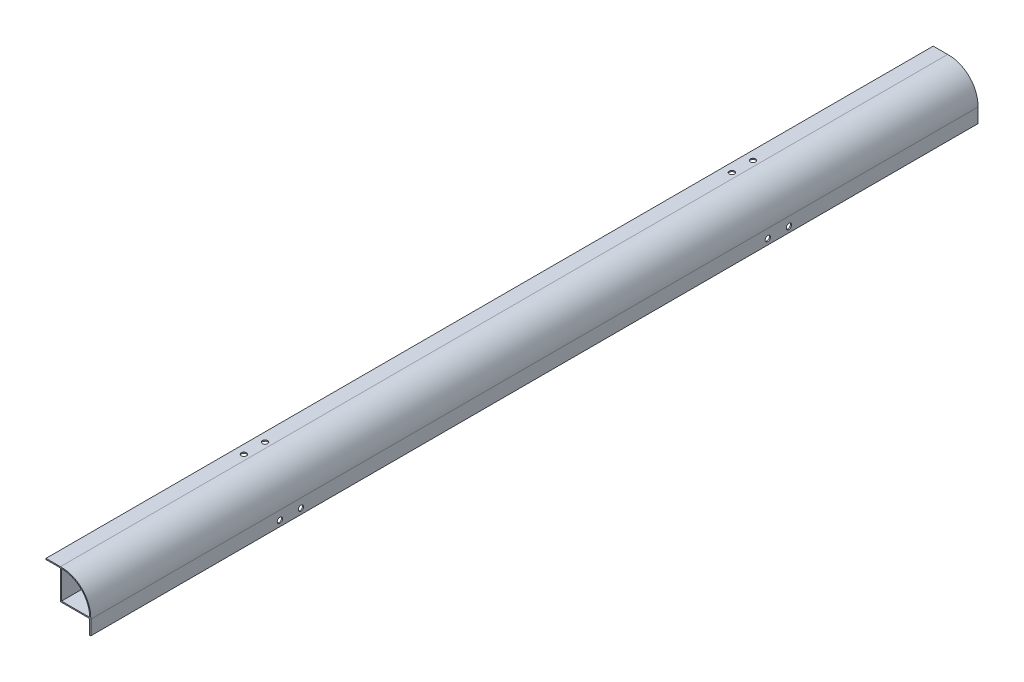
SolidWorks part; units mm, degrees
ref_plane "Alzado" through (0, 0, 0) normal (0, 0, 1) x (1, 0, 0)
ref_plane "Planta" through (0, 0, 0) normal (0, 1, 0) x (1, 0, 0)
ref_plane "Vista lateral" through (0, 0, 0) normal (1, 0, 0) x (0, 0, -1)
sketch "Croquis1" plane through (0, 0, 0) normal (0, 0, 1) x (1, 0, 0)
  line L0 (-13.7, -13.7) -> (13.6811, -13.7)
  line L1 (-12.7, -12.7) -> (12.7, -12.7)
  line L2 (-12.7, -12.7) -> (-12.7, 12.7)
  line L5 (0, 16.5842) -> (0, -23.118) construction
  line L6 (-13.7, -13.7) -> (-13.7, 13.6811)
  line L8 (-18.0998, 0) -> (17.5647, 0) construction
  line L9 (13.6811, -13.7) -> (12.6811, -13.7)
  line L10 (13.6811, -13.7) -> (13.6811, -26.7)
  line L11 (13.6811, -26.7) -> (12.6811, -26.7)
  line L12 (12.6811, -13.7) -> (12.6811, -26.7)
  line L13 (-13.7, 13.6811) -> (-26.7, 13.6811)
  line L14 (-13.7, 13.6811) -> (-13.7, 12.6811)
  line L15 (-13.7, 12.6811) -> (-26.7, 12.6811)
  line L16 (-26.7, 13.6811) -> (-26.7, 12.6811)
  arc A0 (-12.7, 12.7) -> (12.7, -12.7) centre (-12.7, -12.7) cw
  arc A1 (-13.7, 13.6811) -> (13.6811, -13.7) centre (-12.7, -12.7) cw
  point P0 (0, 0)
  point P12 (-12.7, 0)
  point P13 (0, -12.7)
  dimension "D3" = 25.4
  dimension "D1" = 25.4
  dimension "D2" = 25.4
  dimension "D5" = 1
  dimension "D6" = 13
  dimension "D7" = 1
  dimension "D8" = 13
  dimension "D4" = 1
extrude "Saliente-Extruir1" add sketch "Croquis1" along normal mid plane 800 contours A1 L6 L0 L2 A0 L1 | L13 L16 L15 L6 | L0 L12 L11 L10
sketch "Croquis2" plane through (0, 13.6811, 0) normal (0, 1, 0) x (1, 0, 0)
  line L0 (119.3875, 0) -> (-118.4797, 0) construction
  line L1 (-29.9629, -220) -> (20.492, -220) construction
  line L2 (-26.7, -400) -> (-26.7, 400) construction
  line L3 (-13.7, -400) -> (13.7, -400) construction
  line L4 (-29.9629, 220) -> (20.492, 220) construction
  circle A0 centre (-18.7, -210.5) radius 2.3813
  circle A1 centre (-18.7, -229.5) radius 2.3813
  circle A2 centre (-18.7, 229.5) radius 2.3813
  circle A3 centre (-18.7, 210.5) radius 2.3813
  dimension "D1" = 4.7625
  dimension "D2" = 9.5
  dimension "D3" = 8
  dimension "D4" = 180
extrude "Cortar-Extruir1" cut sketch "Croquis2" against normal blind 10
sketch "Croquis3" plane through (13.6811, 0, 0) normal (1, 0, 0) x (0, 0, -1)
  line L0 (0, 76.9116) -> (0, -92.6451) construction
  line L1 (-220, 38.7463) -> (-220, -62.7421) construction
  line L2 (-400, 13.7) -> (-400, -13.7) construction
  line L3 (-400, -26.7) -> (400, -26.7) construction
  line L4 (220, 38.7463) -> (220, -62.7421) construction
  circle A0 centre (-210.5, -21.7) radius 2.3813
  circle A1 centre (-229.5, -21.7) radius 2.3813
  circle A2 centre (-210.5, -21.7) radius 2.3813
  circle A3 centre (-229.5, -21.7) radius 2.3813
  circle A4 centre (229.5, -21.7) radius 2.3813
  circle A5 centre (210.5, -21.7) radius 2.3813
  dimension "D1" = 4.7625
  dimension "D2" = 180
  dimension "D3" = 9.5
  dimension "D4" = 5
extrude "Cortar-Extruir2" cut sketch "Croquis3" against normal blind 10 contours A1 | A0 | A5 | A4
